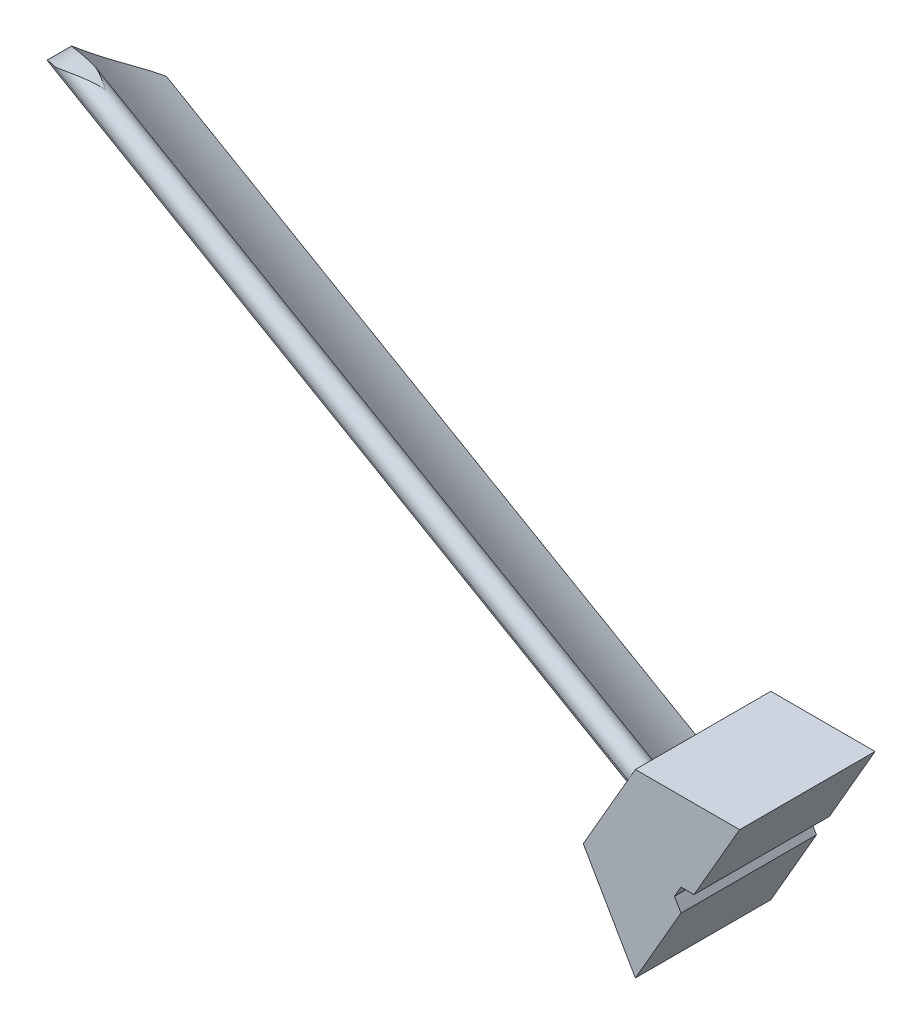
SolidWorks part; units mm, degrees
ref_plane "Ön Düzlem" through (0, 0, 0) normal (0, 0, 1) x (1, 0, 0)
ref_plane "Üst Düzlem" through (0, 0, 0) normal (0, 1, 0) x (1, 0, 0)
ref_plane "Sağ Düzlem" through (0, 0, 0) normal (1, 0, 0) x (0, 0, -1)
sketch "Çizim1" plane through (0, 0, 0) normal (0, 0, 1) x (1, 0, 0)
  line L1 (2.3094, 0) -> (1.1547, 2)
  line L2 (1.1547, 2) -> (-1.1547, 2)
  line L3 (-1.1547, 2) -> (-2.3094, 0)
  line L4 (-2.3094, 0) -> (-1.1547, -2)
  line L5 (-1.1547, -2) -> (1.1547, -2)
  line L6 (1.1547, -2) -> (2.3094, 0)
  line L7 (18.4752, 0) -> (9.2376, 16)
  line L8 (9.2376, 16) -> (-9.2376, 16)
  line L9 (-9.2376, 16) -> (-18.4752, 0)
  line L10 (-18.4752, 0) -> (-9.2376, -16)
  line L11 (-9.2376, -16) -> (9.2376, -16)
  line L12 (9.2376, -16) -> (18.4752, 0)
  circle A0 centre (0, 0) radius 2 construction
  circle A1 centre (0, 0) radius 16 construction
extrude "Yükseklik-Ekstrüzyon1" add sketch "Çizim1" along normal blind 24
sketch "Çizim2" plane through (-13.8564, 8, 0) normal (-0.866, 0.5, 0) x (0, 0, 1)
  arc A0 (20.5667, 8.6325) -> (0.0701, -8.8856) centre (-8.2263, 21.5713) cw
  arc A1 (23.386, 5.7957) -> (20.5667, 8.6325) centre (22, 7.2376) ccw
  arc A2 (0.0701, -8.8856) -> (0.0701, -9.1896) centre (0.2, -9.0376) ccw
  arc A3 (23.386, 5.7957) -> (0.0701, -9.1896) centre (-1.996, 19.6565) cw
extrude "Yükseklik-Ekstrüzyon3" add sketch "Çizim2" along normal blind 120
sketch "Çizim4" plane through (0, 0, 24) normal (0, 0, 1) x (1, 0, 0)
  line L0 (-105.1144, 71.3541) -> (-100.896, 78.5204)
  line L1 (-100.896, 78.5204) -> (-120.0527, 81.5068)
  line L2 (-120.0527, 81.5068) -> (-133.9685, 62.353)
  line L3 (-133.9685, 62.353) -> (-123.7271, 47.8118)
  line L4 (-123.7271, 47.8118) -> (-114.3133, 55.3881)
  arc A1 (-105.1144, 71.3541) -> (-114.3133, 55.3881) centre (-109.7882, 63.414) ccw
extrude "Kes-Ekstrüzyon1" cut sketch "Çizim4" against normal blind 120
sketch "Çizim5" plane through (0, 0, 24) normal (0, 0, 1) x (1, 0, 0)
  line L0 (9.2376, 16) -> (-9.2376, -16)
  line L1 (-9.2376, -16) -> (-9.2376, -28.7404)
  line L2 (-9.2376, -28.7404) -> (42.1998, -28.7404)
  line L3 (42.1998, -28.7404) -> (42.1998, 12.668)
  line L4 (42.1998, 12.668) -> (9.2376, 16)
extrude "Kes-Ekstrüzyon2" cut sketch "Çizim5" against normal blind 120
